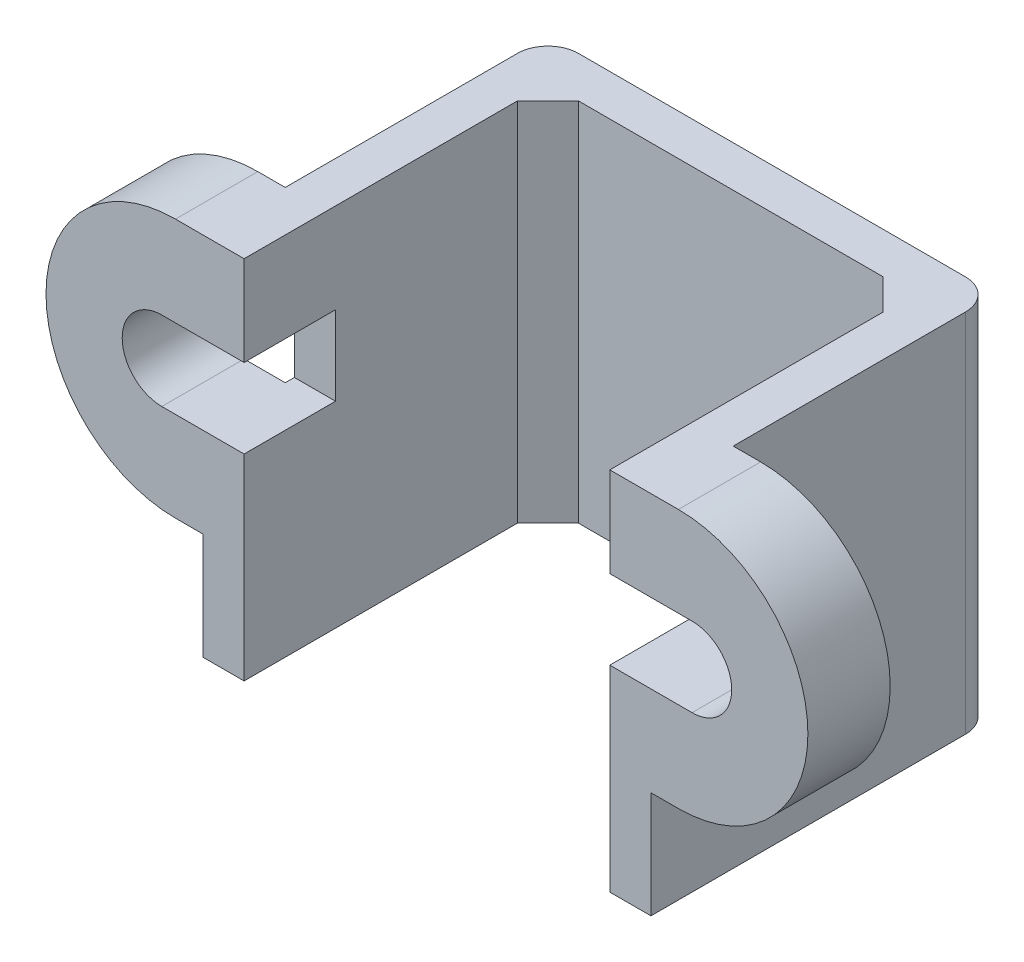
SolidWorks part; units mm, degrees
ref_plane "前视基准面" through (0, 0, 0) normal (0, 0, 1) x (1, 0, 0)
ref_plane "上视基准面" through (0, 0, 0) normal (0, 1, 0) x (1, 0, 0)
ref_plane "右视基准面" through (0, 0, 0) normal (1, 0, 0) x (0, 0, -1)
sketch "草图1" plane through (0, 0, 0) normal (0, 0, 1) x (1, 0, 0)
  line L1 (-6, 6) -> (6, 6)
  line L2 (-6, 6) -> (-6, -6)
  line L3 (-6, -6) -> (6, -6)
  line L4 (6, 6) -> (6, -6)
  line L5 (0, -6) -> (0, 6) construction
  line L6 (-6, 0) -> (6, 0) construction
  point P0 (0, 0)
  dimension "D1" = 12
  dimension "D2" = 12
extrude "凸台-拉伸1" add sketch "草图1" along normal blind 1.35
sketch "草图2" plane through (-6, 0, 0) normal (-1, 0, 0) x (0, 0, 1)
  line L1 (0, 6) -> (11.32, 6)
  line L2 (0, 6) -> (0, -6)
  line L3 (0, -6) -> (11.32, -6)
  line L4 (11.32, 6) -> (11.32, -6)
  dimension "D1" = 11.32
extrude "凸台-拉伸2" add sketch "草图2" along normal blind 1.35
sketch "草图3" plane through (0, 0, 11.32) normal (0, 0, 1) x (1, 0, 0)
  line L0 (-7.35, 6) -> (-8.25, 6)
  line L1 (-8.25, -2.5) -> (-7.35, -2.5)
  line L2 (-7.35, -6) -> (-7.35, 6) construction
  line L3 (-7.35, -2.5) -> (-7.35, 6)
  line L4 (-6, 6) -> (-6, -6) construction
  arc A0 (-8.25, 6) -> (-8.25, -2.5) centre (-8.25, 1.75) ccw
  dimension "D1" = 8.5
  dimension "D2" = 6.5
extrude "凸台-拉伸3" add sketch "草图3" against normal blind 2.7
sketch "草图4" plane through (0, 0, 11.32) normal (0, 0, 1) x (1, 0, 0)
  line L0 (-6, 3.05) -> (-8.7, 3.05)
  line L1 (-6, 6) -> (-6, -6) construction
  line L2 (-8.7, 0.45) -> (-6, 0.45)
  line L3 (-6, -6) -> (-6, 6) construction
  line L4 (-6, 0.45) -> (-6, 3.05)
  arc A0 (-8.7, 3.05) -> (-8.7, 0.45) centre (-8.7, 1.75) ccw
  arc A4 (-8.25, 6) -> (-8.25, -2.5) centre (-8.25, 1.75) ccw construction
  arc A5 (-8.25, 6) -> (-8.25, -2.5) centre (-8.25, 1.75) ccw construction
  dimension "D2" = 4
  dimension "D1" = 2.6
extrude "切除-拉伸1" cut sketch "草图4" against normal blind 3
mirror "镜向1" about plane through (0, 0, 0) normal (1, 0, 0) of "切除-拉伸1", "凸台-拉伸3", "凸台-拉伸2"
chamfer "倒角1" distance 1 angle 45 2 edges at (-6, 0, 1.35) (6, 0, 1.35)
fillet "圆角1" radius 1 2 edges at (7.35, 0, 0) (-7.35, 0, 0)
